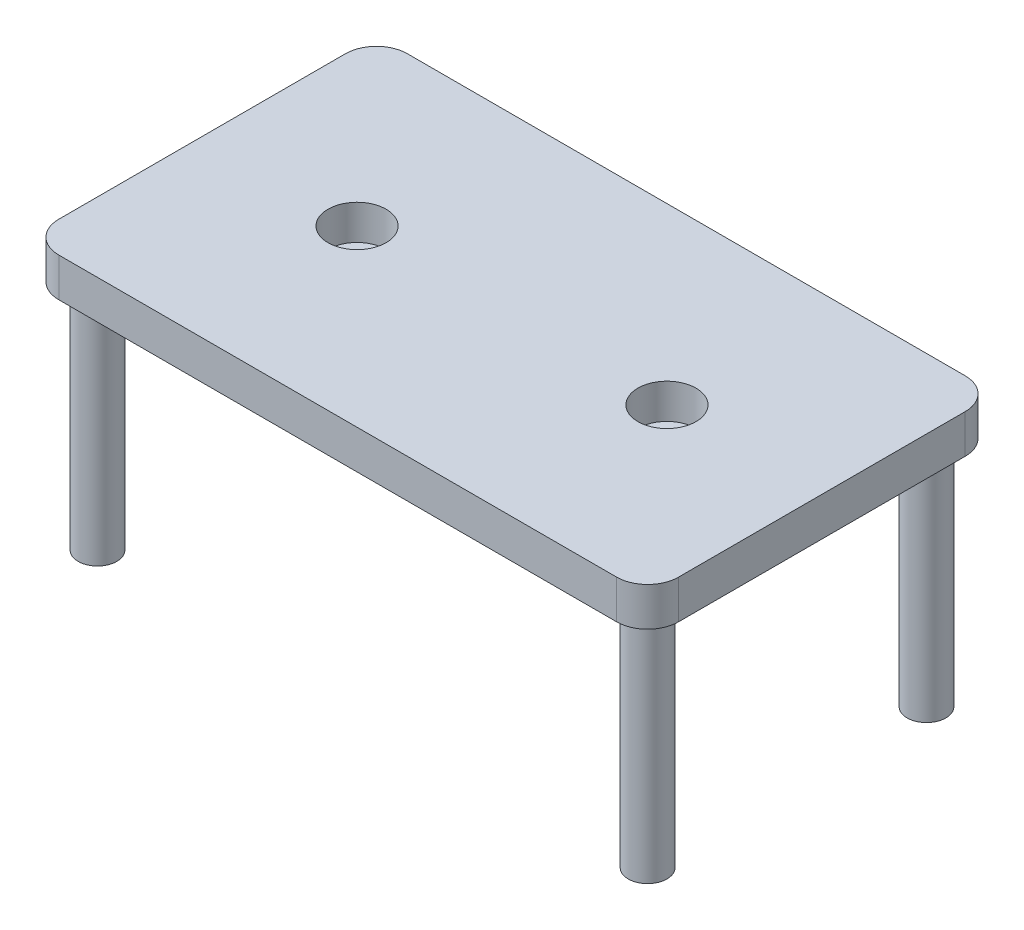
SolidWorks part; units mm, degrees
ref_plane "Front Plane" through (0, 0, 0) normal (0, 0, 1) x (1, 0, 0)
ref_plane "Top Plane" through (0, 0, 0) normal (0, 1, 0) x (1, 0, 0)
ref_plane "Right Plane" through (0, 0, 0) normal (1, 0, 0) x (0, 0, -1)
sketch "Sketch5" plane through (0, 0, 0) normal (0, 1, 0) x (1, 0, 0)
  line L1 (-800, 450) -> (800, 450)
  line L2 (-800, 450) -> (-800, -450)
  line L3 (-800, -450) -> (800, -450)
  line L4 (800, 450) -> (800, -450)
  line L5 (-800, 450) -> (800, -450) construction
  line L6 (-800, -450) -> (800, 450) construction
  point P0 (0, 0)
  dimension "D1" = 1600
  dimension "D2" = 900
extrude "Boss-Extrude4" add sketch "Sketch5" along normal blind 100
sketch "Sketch6" plane through (0, 100, 0) normal (0, 1, 0) x (1, 0, 0)
  line L0 (0, 450) -> (0, -450) construction
  line L1 (800, 450) -> (-800, 450) construction
  line L2 (-800, -450) -> (800, -450) construction
  line L3 (0, 0) -> (-800, 0) construction
  line L4 (-800, 450) -> (-800, -450) construction
  line L5 (-800, 0) -> (800, 0) construction
  line L6 (800, -450) -> (800, 450) construction
  circle A0 centre (-710, 360) radius 50
  circle A1 centre (710, 360) radius 50
  circle A2 centre (710, -360) radius 50
  circle A3 centre (-710, -360) radius 50
  dimension "D1" = 100
  dimension "D2" = 90
  dimension "D3" = 90
extrude "Boss-Extrude5" add sketch "Sketch6" against normal blind 700
sketch "Sketch8" plane through (0, 100, 0) normal (0, 1, 0) x (1, 0, 0)
  line L0 (0, 450) -> (0, -450) construction
  line L1 (800, 450) -> (-800, 450) construction
  line L2 (-800, -450) -> (800, -450) construction
  line L3 (0, 0) -> (800, 0) construction
  line L4 (800, -450) -> (800, 450) construction
  circle A1 centre (400, 0) radius 75
  dimension "D1" = 150
extrude "Cut-Extrude2" cut sketch "Sketch8" against normal blind 90
mirror "Mirror1" about plane through (0, 0, 0) normal (1, 0, 0) of "Cut-Extrude2"
fillet "Fillet2" radius 80 4 edges at (-800, 50, -450) (800, 50, -450) (800, 50, 450) (-800, 50, 450)
